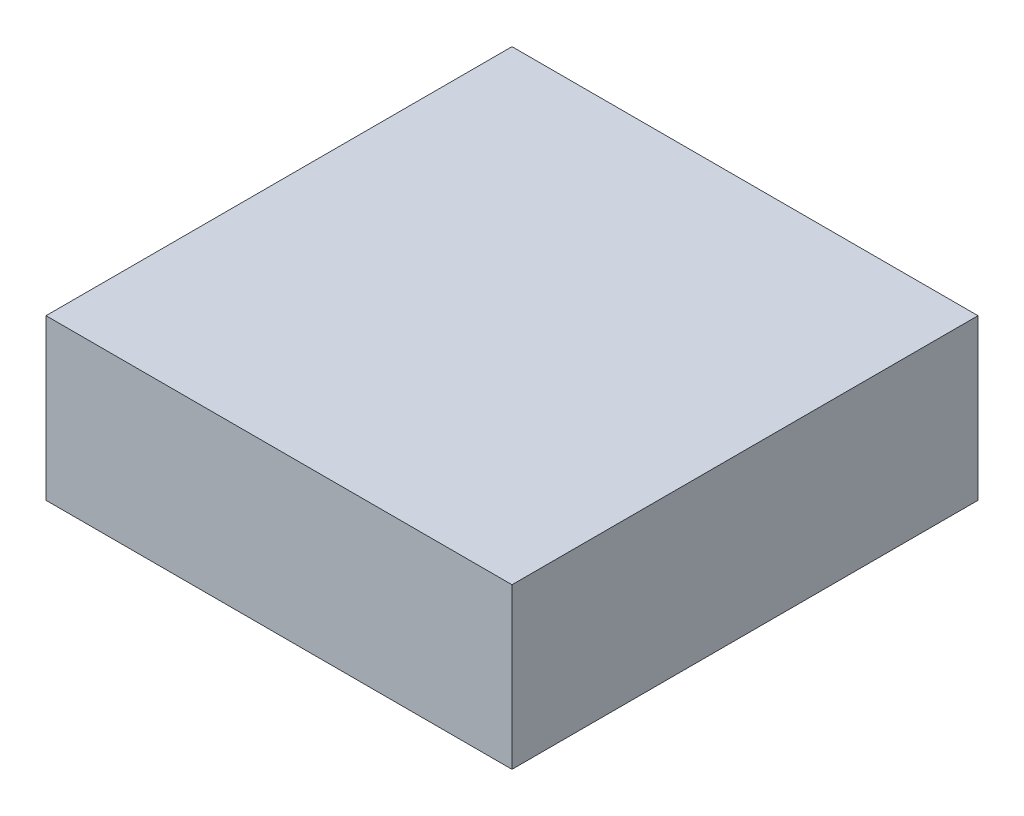
SolidWorks part; units mm, degrees
ref_plane "Front Plane" through (0, 0, 0) normal (0, 0, 1) x (1, 0, 0)
ref_plane "Top Plane" through (0, 0, 0) normal (0, 1, 0) x (1, 0, 0)
ref_plane "Right Plane" through (0, 0, 0) normal (1, 0, 0) x (0, 0, -1)
sketch "Sketch1" plane through (0, 0, 0) normal (0, 1, 0) x (1, 0, 0)
  line L1 (0, 0) -> (102, 0)
  line L2 (0, 0) -> (0, 102)
  line L3 (0, 102) -> (102, 102)
  line L4 (102, 0) -> (102, 102)
  dimension "D1" = 102
extrude "Boss-Extrude1" add sketch "Sketch1" along normal blind 35
